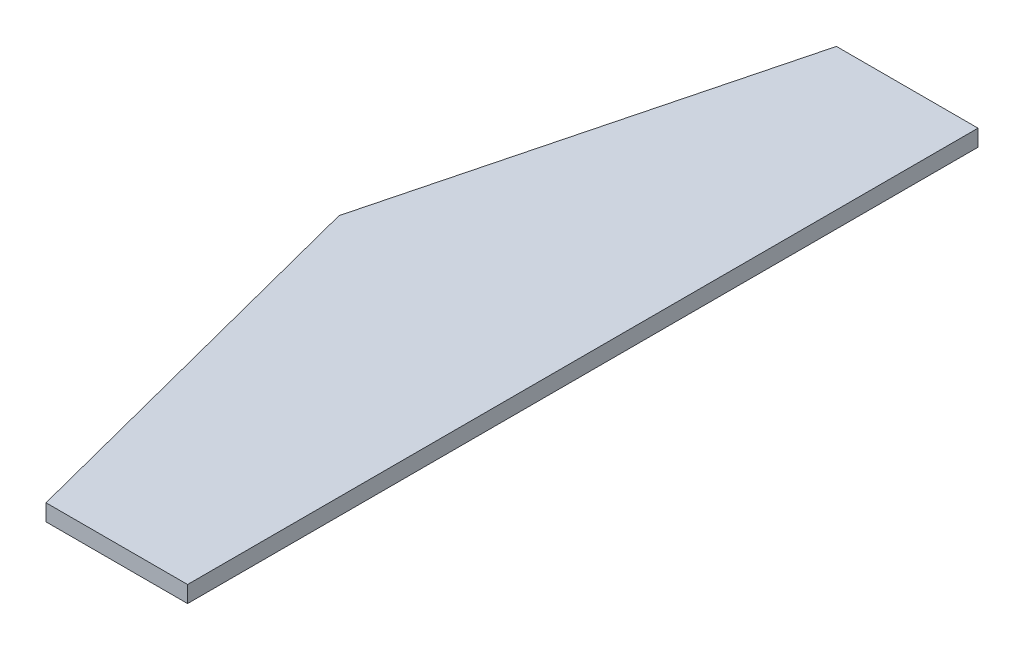
SolidWorks part; units mm, degrees
ref_plane "Front Plane" through (0, 0, 0) normal (0, 0, 1) x (1, 0, 0)
ref_plane "Top Plane" through (0, 0, 0) normal (0, 1, 0) x (1, 0, 0)
ref_plane "Right Plane" through (0, 0, 0) normal (1, 0, 0) x (0, 0, -1)
sketch "Sketch1" plane through (0, 0, 0) normal (0, 1, 0) x (1, 0, 0)
  line L0 (0, 646.6659) -> (0, -646.6659) construction
  line L1 (0, 430.2965) -> (0, -286.4035)
  line L2 (0, -286.4035) -> (-128.3717, -286.4035)
  line L3 (-128.3717, -286.4035) -> (-220.9873, 71.9465)
  line L4 (-220.9873, 71.9465) -> (-128.3717, 430.2965)
  line L5 (-128.3717, 430.2965) -> (0, 430.2965)
  line L6 (626.5324, 71.9465) -> (-1068.5069, 71.9465) construction
  line L7 (-182.5, 220.8623) -> (0, 220.8623) construction
  point P4 (0, 0)
  point P7 (0, 71.9465)
  point P22 (-220.9873, 71.9465)
  dimension "D1" = 716.7
  dimension "D2" = 182.5
extrude "Boss-Extrude1" add sketch "Sketch1" along normal blind 15
